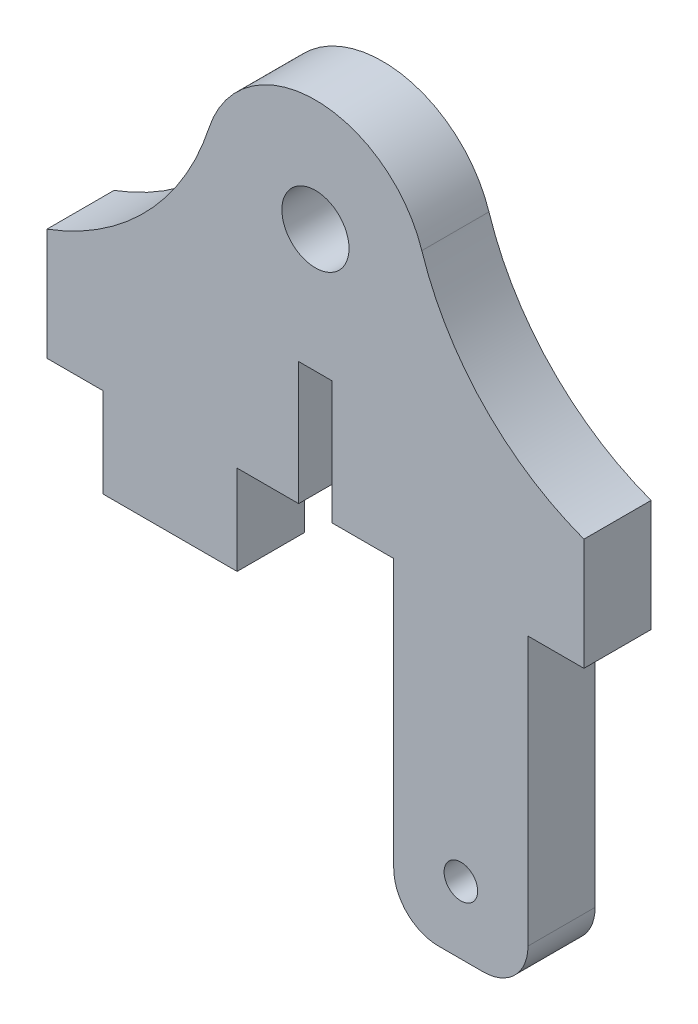
SolidWorks part; units mm, degrees
material "PMMA"
ref_plane "Front Plane" through (0, 0, 0) normal (0, 0, 1) x (1, 0, 0)
ref_plane "Top Plane" through (0, 0, 0) normal (0, 1, 0) x (1, 0, 0)
ref_plane "Right Plane" through (0, 0, 0) normal (1, 0, 0) x (0, 0, -1)
sketch "Sketch1" plane through (0, 0, 0) normal (0, 0, 1) x (1, 0, 0)
  line L0 (0, 0) -> (0, -5.5) construction
  line L1 (-0.75, -11) -> (-7, -11)
  line L2 (-12, -11) -> (-12, -6)
  line L3 (0.75, -11) -> (3.5, -11)
  line L4 (3.5, -11) -> (3.5, -25)
  line L5 (3.5, -25) -> (12, -25)
  line L6 (12, -25) -> (12, -6)
  line L7 (-0.75, -11) -> (-0.75, -5.5)
  line L8 (-0.75, -5.5) -> (0.75, -5.5)
  line L9 (0.75, -5.5) -> (0.75, -11)
  line L10 (-12, -11) -> (-12, -15)
  line L11 (-12, -15) -> (-7, -15)
  line L12 (-7, -15) -> (-7, -11)
  circle A0 centre (0, 0) radius 1.5
  arc A1 (4.7553, 1.545) -> (-4.7553, 1.545) centre (0, 0) ccw
  arc A2 (-12, -6) -> (-4.7553, 1.545) centre (-16.1681, 5.2529) ccw
  arc A3 (12, -6) -> (4.7553, 1.545) centre (16.1681, 5.2529) cw
  circle A6 centre (6.5, -22) radius 0.75
  point P20 (12, -25)
  point P23 (3.5, -25)
  dimension "D1" = 3
  dimension "D2" = 11
  dimension "D6" = 12
  dimension "D3" = 5
  dimension "D15" = 1.5
  dimension "D4" = 11
  dimension "D5" = 5
  dimension "D7" = 12
  dimension "D8" = 8.5
  dimension "D9" = 1.5
  dimension "D10" = 0.75
  dimension "D11" = 5.5
  dimension "D12" = 14
  dimension "D14" = 11
  dimension "D16" = 6.5
  dimension "D17" = 5
  dimension "D18" = 4
  dimension "D19" = 15
extrude "Boss-Extrude1" add sketch "Sketch1" along normal blind 3
cosmetic thread "Cosmetic Thread1" parameters "D2"=2
sketch "Sketch2" plane through (0, 0, 3) normal (0, 0, 1) x (1, 0, 0)
  line L1 (-12, -15) -> (-9.5, -15)
  line L2 (-12, -15) -> (-12, -11)
  line L3 (-12, -11) -> (-9.5, -11)
  line L4 (-9.5, -15) -> (-9.5, -11)
  dimension "D1" = 4
  dimension "D2" = 2.5
extrude "Cut-Extrude1" cut sketch "Sketch2" against normal blind 10
sketch "Sketch3" plane through (0, 0, 3) normal (0, 0, 1) x (1, 0, 0)
  line L0 (-7, -11) -> (-0.75, -11) construction
  line L1 (-7, -15) -> (-3.5, -15)
  line L2 (-7, -15) -> (-7, -11)
  line L3 (-7, -11) -> (-3.5, -11)
  line L4 (-3.5, -15) -> (-3.5, -11)
  dimension "D1" = 3.5
extrude "Boss-Extrude2" add sketch "Sketch3" against normal up to surface (3 mm away) up to face at (-1.625, -10.2573, 0)
sketch "Sketch4" plane through (0, 0, 3) normal (0, 0, 1) x (1, 0, 0)
  line L0 (-9.5, -15) -> (-3.5, -15) construction
  line L1 (12, -25) -> (9.5, -25)
  line L2 (12, -25) -> (12, -11)
  line L3 (12, -11) -> (9.5, -11)
  line L4 (9.5, -25) -> (9.5, -11)
  dimension "D1" = 2.5
  dimension "D2" = 4
extrude "Cut-Extrude2" cut sketch "Sketch4" against normal blind 10
fillet "Fillet1" radius 2 2 edges at (3.5, -25, 1.5) (9.5, -25, 1.5)
